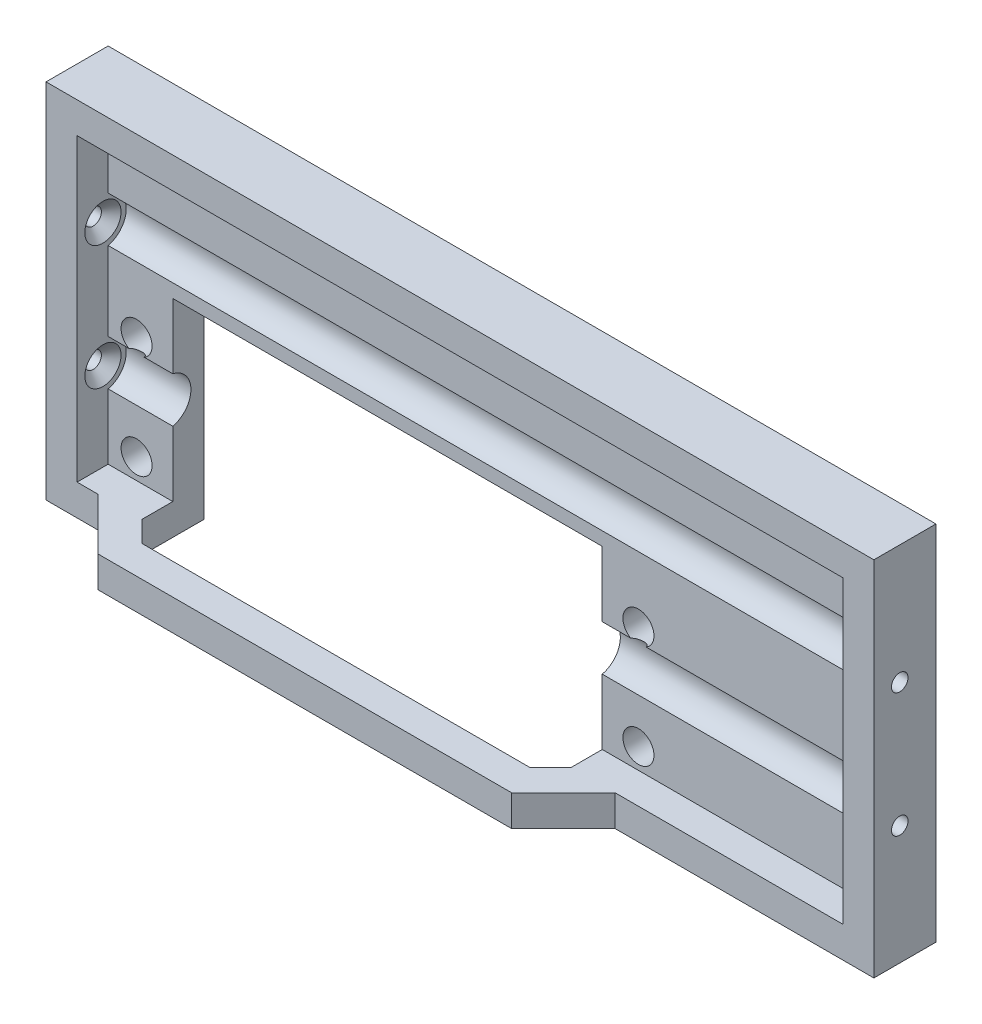
SolidWorks part; units mm, degrees
material "PVC hart"
ref_plane "Ebene vorne" through (0, 0, 0) normal (0, 0, 1) x (1, 0, 0)
ref_plane "Ebene oben" through (0, 0, 0) normal (0, 1, 0) x (1, 0, 0)
ref_plane "Ebene rechts" through (0, 0, 0) normal (1, 0, 0) x (0, 0, -1)
sketch "Skizze2" plane through (0, 0, 0) normal (0, 1, 0) x (1, 0, 0)
  line L0 (-40, 0) -> (40, 0)
  line L1 (-40, 0) -> (-40, -6)
  line L2 (-40, -6) -> (-37, -6)
  line L3 (-37, -6) -> (-37, -3)
  line L4 (-37, -3) -> (37, -3)
  line L5 (37, -3) -> (37, -6)
  line L6 (37, -6) -> (40, -6)
  line L7 (40, -6) -> (40, 0)
  line L8 (0, 0) -> (0, -3) construction
  dimension "D1" = 6
  dimension "D2" = 3
  dimension "D3" = 3
  dimension "D4" = 80
extrude "Aufsatz-Linear austragen2" add sketch "Skizze2" along normal mid plane 35
sketch "Skizze3" plane through (0, 0, 3) normal (0, 0, 1) x (1, 0, 0)
  line L0 (-37, -17.5) -> (37, -17.5) construction
  line L1 (-30.75, 2.5) -> (10.75, 2.5)
  line L2 (-30.75, 2.5) -> (-30.75, -17.5)
  line L3 (-30.75, -17.5) -> (10.75, -17.5)
  line L4 (10.75, 2.5) -> (10.75, -17.5)
  line L5 (-34.25, -2.5) -> (-34.25, -12.5) construction
  line L6 (14.25, -2.5) -> (14.25, -12.5) construction
  line L7 (-34.25, -7.5) -> (-30.75, -7.5) construction
  line L8 (10.75, -7.5) -> (14.25, -7.5) construction
  line L9 (-30.75, -7.5) -> (0, -7.5) construction
  line L10 (0, -7.5) -> (10.75, -7.5) construction
  line L11 (0, 17.5) -> (0, -17.5) construction
  line L12 (-37, 17.5) -> (37, 17.5) construction
  circle A0 centre (-34.25, -2.5) radius 1.5
  circle A1 centre (-34.25, -12.5) radius 1.5
  circle A2 centre (14.25, -2.5) radius 1.5
  circle A3 centre (14.25, -12.5) radius 1.5
  point P18 (0, -7.5)
  dimension "D2" = 3
  dimension "D1" = 10
  dimension "D3" = 48.5
  dimension "D4" = 41.5
  dimension "D5" = 20
  dimension "D6" = 14.25
extrude "Schnitt-Linear austragen1" cut sketch "Skizze3" against normal through all
sketch "Skizze4" plane through (0, 0, 3) normal (0, 0, 1) x (1, 0, 0)
  line L0 (37, 17.5) -> (37, -17.5) construction
  line L1 (-37, 17.5) -> (37, 17.5)
  line L2 (-37, 17.5) -> (-37, 14.5)
  line L3 (-37, 14.5) -> (37, 14.5)
  line L4 (37, 17.5) -> (37, 14.5)
  line L6 (-40, 17.5) -> (-37, 17.5) construction
extrude "Aufsatz-Linear austragen3" add sketch "Skizze4" along normal up to surface (3 mm away) up to face at (38.5, 0, 6)
sketch "Skizze5" plane through (0, -17.5, 0) normal (0, -1, 0) x (1, 0, 0)
  line L0 (-37, 6) -> (-34.9926, 6)
  line L1 (37, 6) -> (-37, 6) construction
  line L2 (-34.9926, 6) -> (-29.9926, 11)
  line L3 (-29.9926, 11) -> (9.9926, 11)
  line L4 (9.9926, 11) -> (14.9926, 6)
  line L5 (14.9926, 6) -> (37, 6)
  line L6 (37, 6) -> (37, 3)
  line L7 (37, 3) -> (10.75, 3)
  line L8 (10.75, 3) -> (10.75, 6)
  line L9 (10.75, 6) -> (8.75, 8)
  line L10 (8.75, 8) -> (-28.75, 8)
  line L11 (-28.75, 8) -> (-30.75, 6)
  line L12 (-30.75, 6) -> (-30.75, 3)
  line L13 (-37, 3) -> (37, 3) construction
  line L14 (-37, 6) -> (-37, 3)
  line L15 (-37, 3) -> (-30.75, 3)
  line L16 (10.75, 3) -> (-30.75, 3) construction
  line L17 (-10, 11) -> (-10, 8) construction
  line L18 (-10, 8) -> (-10, 3) construction
  line L21 (-32.4926, 8.5) -> (-30.3713, 6.3787) construction
  dimension "D1" = 135
  dimension "D2" = 3
  dimension "D3" = 5
extrude "Aufsatz-Linear austragen4" add sketch "Skizze5" against normal blind 3
hole_wizard "Formsenkung für M3 Senkschraube mit Innensechskant1" positions "Skizze7" profile "Skizze6" countersink size "M3" standard "DIN"
sketch "Skizze7" plane through (-37, 0, 0) normal (1, 0, 0) x (0, 0, -1)
  line L0 (-3.5, 6) -> (-3.5, -6) construction
  line L2 (-3.5, 0) -> (-6, 0) construction
  line L3 (-6, 14.5) -> (-6, -14.5) construction
  point P0 (-3.5, 6)
  point P2 (-3.5, -6)
  dimension "D1" = 12
  dimension "D2" = 2.5
sketch "Skizze6" plane through (-37, 6, 3.5) normal (0, 1, 0) x (0, 0, -1)
  line L0 (0, 0) -> (0, 3)
  line L1 (0, 3) -> (0.8, 3)
  line L2 (0.8, 3) -> (0.8, 0.95)
  line L3 (0.8, 0.95) -> (1.75, 0)
  line L5 (1.75, 0) -> (0, 0)
  line L6 (-0.8, 0.95) -> (-1.75, 0) construction
  line L11 (0, -6.35) -> (0, 107.95) construction
  dimension "Bohrerdurchmesser" = 1.6
  dimension "Bohrungstiefe" = 3
  dimension "Senkdurchmesser (Oben)" = 3.5
  dimension "Senkwinkel (Oben)" = 90
sketch "Skizze8" plane through (-37, 0, 0) normal (1, 0, 0) x (0, 0, -1)
  circle A6 centre (-3.5, -6) radius 2.25
  circle A7 centre (-3.5, 6) radius 2.25
  arc A8 (-3, 7.6771) -> (-3, 4.3229) centre (-3.5, 6) ccw construction
  dimension "D1" = 0.5
extrude "Schnitt-Linear austragen2" cut sketch "Skizze8" along normal up to surface (74 mm away) up to face at (37, 0, 4.5)
mirror "Spiegeln2" about plane through (0, 0, 0) normal (1, 0, 0) of "Formsenkung für M3 Senkschraube mit Innensechskant1"
